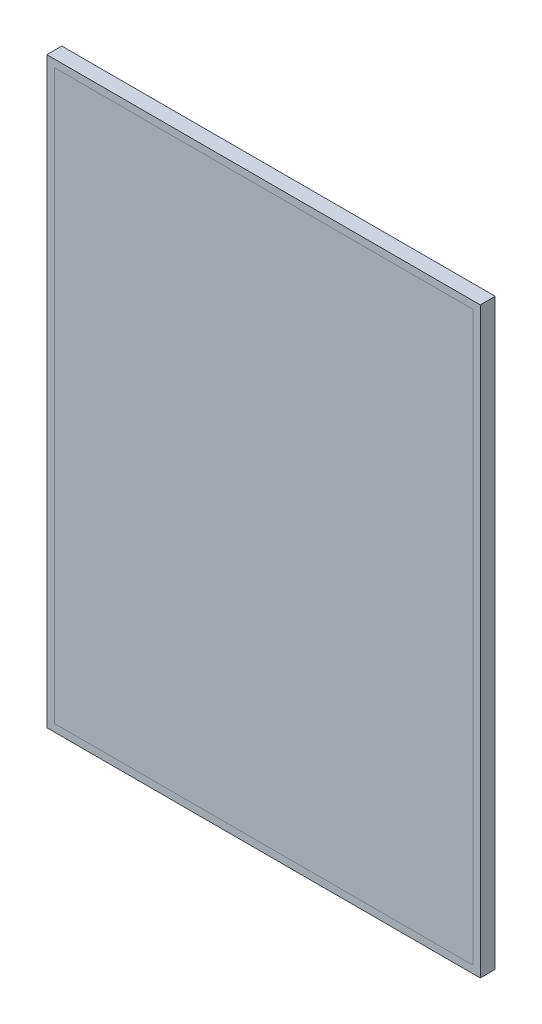
SolidWorks part; units mm, degrees
ref_plane "Front Plane" through (0, 0, 0) normal (0, 0, 1) x (1, 0, 0)
ref_plane "Top Plane" through (0, 0, 0) normal (0, 1, 0) x (1, 0, 0)
ref_plane "Right Plane" through (0, 0, 0) normal (1, 0, 0) x (0, 0, -1)
sketch "Sketch1" plane through (0, 0, 0) normal (0, 0, 1) x (1, 0, 0)
  line L1 (-145, 195) -> (145, 195)
  line L2 (-145, 195) -> (-145, -195)
  line L3 (-145, -195) -> (145, -195)
  line L4 (145, 195) -> (145, -195)
  line L5 (-145, 195) -> (145, -195) construction
  line L6 (-145, -195) -> (145, 195) construction
  line L7 (-140, 190) -> (140, 190)
  line L8 (-140, 190) -> (-140, -190)
  line L9 (-140, -190) -> (140, -190)
  line L10 (140, 190) -> (140, -190)
  line L11 (-140, 190) -> (140, -190) construction
  line L12 (-140, -190) -> (140, 190) construction
  point P0 (0, 0)
  point P6 (0, 0)
  dimension "D1" = 390
  dimension "D2" = 290
  dimension "D3" = 380
  dimension "D4" = 280
extrude "Boss-Extrude1" add sketch "Sketch1" along normal blind 10
sketch "Sketch2" plane through (0, 0, 10) normal (0, 0, 1) x (1, 0, 0)
  line L1 (-140, 190) -> (140, 190)
  line L2 (-140, 190) -> (-140, -190)
  line L3 (-140, -190) -> (140, -190)
  line L4 (140, 190) -> (140, -190)
  line L5 (-140, 190) -> (140, -190) construction
  line L6 (-140, -190) -> (140, 190) construction
  point P0 (0, 0)
extrude "Boss-Extrude2" add sketch "Sketch2" against normal blind 1 separate body
